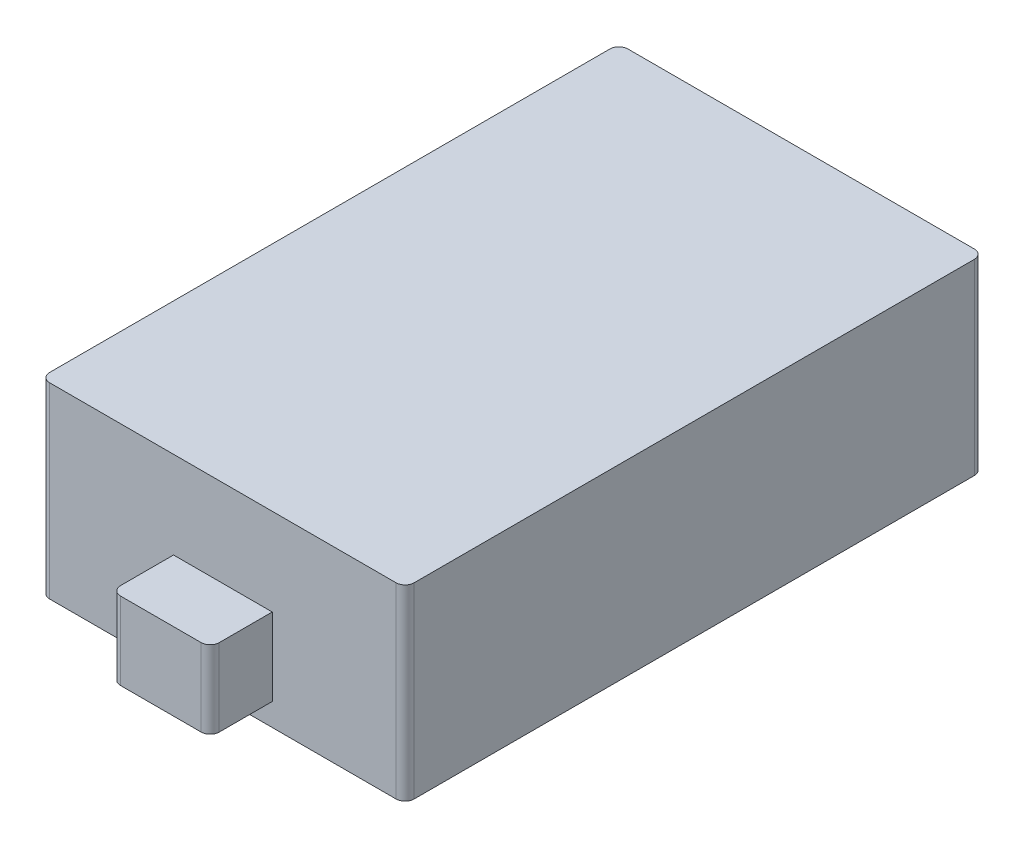
SolidWorks part; units mm, degrees
ref_plane "Front Plane" through (0, 0, 0) normal (0, 0, 1) x (1, 0, 0)
ref_plane "Top Plane" through (0, 0, 0) normal (0, 1, 0) x (1, 0, 0)
ref_plane "Right Plane" through (0, 0, 0) normal (1, 0, 0) x (0, 0, -1)
sketch "Sketch1" plane through (0, 0, 0) normal (0, 1, 0) x (1, 0, 0)
  line L2 (16.15, -25.625) -> (-16.15, -25.625)
  line L3 (16.15, -25.625) -> (16.15, 25.625)
  line L4 (16.15, 25.625) -> (-16.15, 25.625)
  line L5 (-16.15, -25.625) -> (-16.15, 25.625)
  line L6 (16.15, -25.625) -> (-16.15, 25.625) construction
  line L7 (16.15, 25.625) -> (-16.15, -25.625) construction
  point P2 (0, 0)
  dimension "D1" = 32.3
  dimension "D2" = 51.25
extrude "Boss-Extrude2" add sketch "Sketch1" along normal blind 16.6
sketch "Sketch2" plane through (0, 0, 25.625) normal (0, 0, 1) x (1, 0, 0)
  line L0 (17.765, 0) -> (-17.765, 0) construction
  line L1 (4.375, 2) -> (-4.375, 2)
  line L2 (4.375, 2) -> (4.375, 8.87)
  line L3 (4.375, 8.87) -> (-4.375, 8.87)
  line L4 (-4.375, 2) -> (-4.375, 8.87)
  line L5 (4.375, 2) -> (-4.375, 8.87) construction
  line L6 (4.375, 8.87) -> (-4.375, 2) construction
  line L7 (-16.15, 16.6) -> (-16.15, 0) construction
  point P0 (0, 5.435)
  dimension "D1" = 8.75
  dimension "D2" = 6.87
  dimension "D3" = 2
  dimension "D4" = 11.775
extrude "Boss-Extrude3" add sketch "Sketch2" along normal blind 5.5
sketch "Sketch3" plane through (0, 0, -25.625) normal (0, 0, -1) x (-1, 0, 0)
  line L0 (4.375, 2) -> (-4.375, 2)
  line L1 (4.375, 2) -> (4.375, 8.9295)
  line L2 (4.375, 8.9295) -> (-4.375, 8.9295)
  line L3 (-4.375, 2) -> (-4.375, 8.9295)
  line L4 (-16.15, 16.6) -> (-16.15, 0) construction
  line L5 (17.765, 0) -> (-17.765, 0) construction
  dimension "D1" = 11.775
  dimension "D2" = 2
extrude "Boss-Extrude4" add sketch "Sketch3" along normal blind 5.5
fillet "Fillet1" radius 0.8 8 edges at (-4.375, 5.435, 31.125) (4.375, 5.435, 31.125) (16.15, 8.3, 25.625) (-16.15, 8.3, 25.625) (16.15, 8.3, -25.625) (-16.15, 8.3, -25.625) (-4.375, 5.4647, -31.125) (4.375, 5.4647, -31.125)
